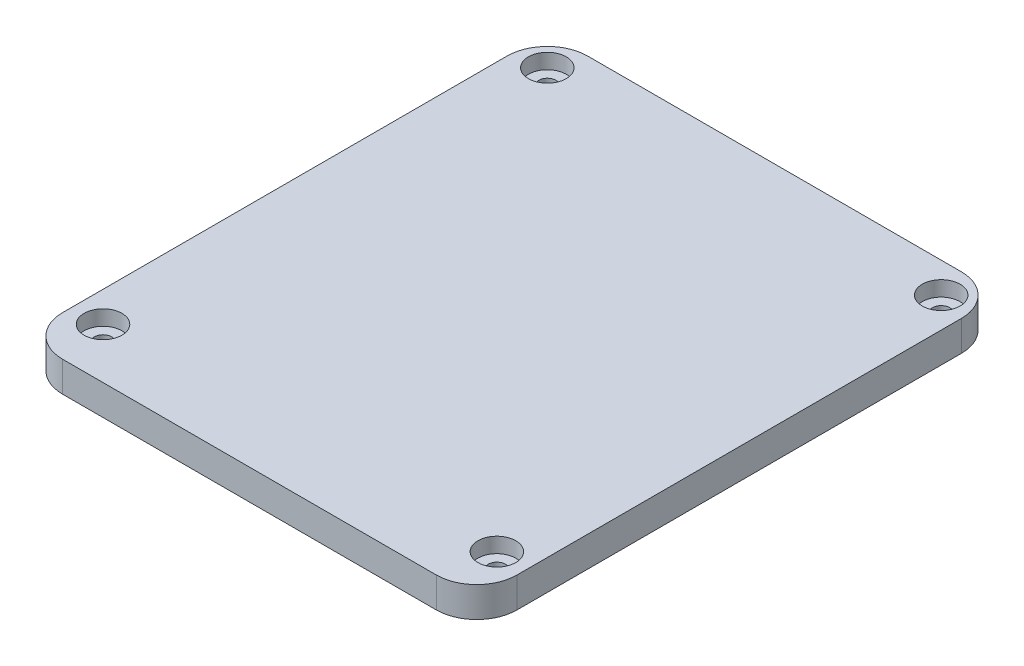
SolidWorks part; units mm, degrees
ref_plane "Спереди" through (0, 0, 0) normal (0, 0, 1) x (1, 0, 0)
ref_plane "Сверху" through (0, 0, 0) normal (0, 1, 0) x (1, 0, 0)
ref_plane "Справа" through (0, 0, 0) normal (1, 0, 0) x (0, 0, -1)
sketch "Sketch1" plane through (0, 0, 0) normal (0, 1, 0) x (1, 0, 0)
  line L1 (45, -50) -> (-45, -50)
  line L2 (45, -50) -> (45, 50)
  line L3 (45, 50) -> (-45, 50)
  line L4 (-45, -50) -> (-45, 50)
  line L5 (45, -50) -> (-45, 50) construction
  line L6 (45, 50) -> (-45, -50) construction
  point P0 (0, 0)
  dimension "D1" = 90
  dimension "D2" = 100
extrude "Boss-Extrude1" add sketch "Sketch1" along normal blind 3
sketch "Sketch2" plane through (0, 3, 0) normal (0, 1, 0) x (1, 0, 0)
  line L0 (-45, 50) -> (-45, -50) construction
  line L1 (39, -44) -> (-39, -44) construction
  line L2 (39, -44) -> (39, 44) construction
  line L3 (39, 44) -> (-39, 44) construction
  line L4 (-39, -44) -> (-39, 44) construction
  line L5 (39, -44) -> (-39, 44) construction
  line L6 (39, 44) -> (-39, -44) construction
  line L7 (45, 50) -> (-45, 50) construction
  circle A0 centre (-39, 44) radius 1.7
  circle A1 centre (39, 44) radius 1.7
  circle A2 centre (39, -44) radius 1.7
  circle A3 centre (-39, -44) radius 1.7
  point P0 (0, 0)
  dimension "D3" = 3.4
  dimension "D1" = 6
  dimension "D2" = 6
extrude "Cut-Extrude1" cut sketch "Sketch2" against normal through all
sketch "Sketch4" plane through (0, 0, 0) normal (0, -1, 0) x (1, 0, 0)
  line L0 (-45, -50) -> (-45, 50) construction
  line L1 (41.6, 46.6) -> (-39.6, 46.6)
  line L2 (41.6, 46.6) -> (41.6, -46.6)
  line L3 (41.6, -46.6) -> (-39.6, -46.6)
  line L4 (-39.6, 46.6) -> (-39.6, -46.6)
  line L5 (-45, 50) -> (45, 50) construction
  line L6 (45, 50) -> (45, -50) construction
  line L7 (45, -50) -> (-45, -50) construction
  line L9 (38.6, 43.6) -> (-36.6, 43.6)
  line L10 (38.6, 43.6) -> (38.6, -43.6)
  line L11 (38.6, -43.6) -> (-36.6, -43.6)
  line L12 (-36.6, 43.6) -> (-36.6, -43.6)
  point P0 (0, 0)
  point P10 (0, 0)
  dimension "D1" = 5.4
  dimension "D2" = 3.4
  dimension "D3" = 3
  dimension "D4" = 3
  dimension "D5" = 3
  dimension "D6" = 3.4
  dimension "D7" = 3
  dimension "D8" = 3.4
extrude "Boss-Extrude2" add sketch "Sketch4" along normal blind 2
sketch "Sketch6" plane through (0, 3, 0) normal (0, 1, 0) x (1, 0, 0)
  line L0 (45, -50) -> (45, 50) construction
  circle A0 centre (-39, 44) radius 6
  circle A1 centre (-39, -44) radius 6
  circle A2 centre (39, -44) radius 6
  circle A3 centre (39, 44) radius 6
extrude "Cut-Extrude5" cut sketch "Sketch6" against normal through all from offset 3 offset against normal yes
sketch "Sketch7" plane through (0, 0, 50) normal (0, 0, 1) x (1, 0, 0)
  line L0 (-45, 3) -> (-45, 0)
  line L1 (-45, 0) -> (45, 0)
  line L2 (45, 0) -> (45, 3)
  line L3 (45, 3) -> (-45, 3)
extrude "Boss-Extrude3" add sketch "Sketch7" along normal blind 4
sketch "Sketch8" plane through (0, 3, 0) normal (0, 1, 0) x (1, 0, 0)
  line L0 (-45, -50) -> (-45, -54)
  line L1 (-45, -54) -> (45, -54)
  line L2 (45, -50) -> (45, 50)
  line L3 (45, 50) -> (-45, 50)
  line L4 (-45, -50) -> (-45, 50)
  line L5 (45, -50) -> (-45, 50) construction
  line L6 (45, 50) -> (-45, -50) construction
  line L7 (45, -54) -> (45, -50)
  circle A1 centre (-39, 44) radius 3.75
  circle A3 centre (39, 44) radius 3.75
  circle A6 centre (-39, -44) radius 3.75
  circle A7 centre (39, -44) radius 3.75
  point P0 (0, 0)
  dimension "D1" = 7.5
extrude "Boss-Extrude4" add sketch "Sketch8" along normal blind 3
fillet "Fillet1" radius 8 4 edges at (-45, 3, -50) (-45, 3, 54) (45, 3, -50) (45, 3, 54)
